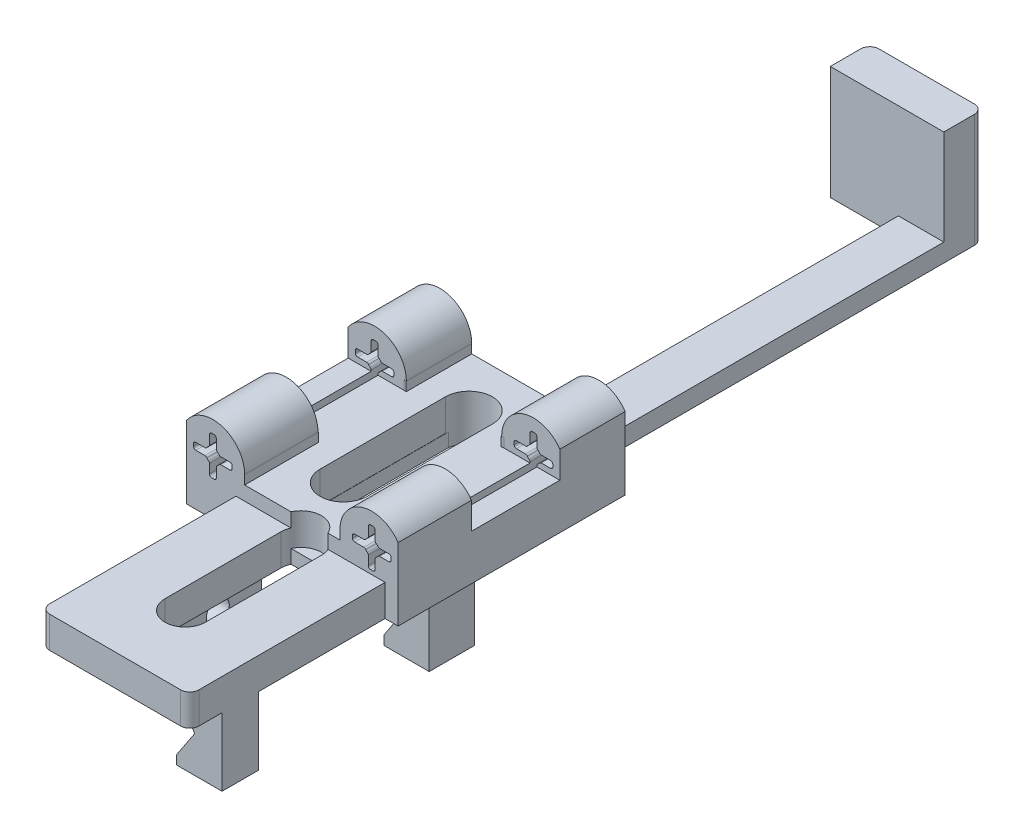
SolidWorks part; units mm, degrees
ref_plane "Спереди" through (0, 0, 0) normal (0, 0, 1) x (1, 0, 0)
ref_plane "Сверху" through (0, 0, 0) normal (0, 1, 0) x (1, 0, 0)
ref_plane "Справа" through (0, 0, 0) normal (1, 0, 0) x (0, 0, -1)
sketch "Эскиз1" plane through (0, 0, 0) normal (0, 0, 1) x (1, 0, 0)
  line L0 (19.0011, -5) -> (13.1937, -5)
  line L1 (17.2564, -4.2433) -> (15.2847, -4.2433)
  line L2 (15.2853, -5.7567) -> (17.2564, -5.7567)
  line L3 (18.2444, -6.7448) -> (18.2444, -8.7164)
  line L5 (19.2579, -9.2566) -> (18.7444, -9.2566)
  line L7 (19.7579, -8.7158) -> (19.7579, -6.7448)
  line L10 (13.1937, -5) -> (54.9814, -5)
  line L12 (13.1937, -14) -> (59.7886, -14)
  line L15 (26.0011, -5) -> (54.9814, -5)
  line L16 (20.7459, -5.7567) -> (22.7175, -5.7567)
  line L17 (13.1937, -5) -> (59.7886, -5)
  line L18 (23.2577, -4.7433) -> (23.2577, -5.2567)
  line L19 (22.717, -4.2433) -> (20.7459, -4.2433)
  line L20 (19.7579, -3.2552) -> (19.7579, -1.2836)
  line L21 (18.7444, -0.7434) -> (19.2579, -0.7434)
  line L22 (18.2444, -1.2842) -> (18.2444, -3.2552)
  line L26 (36.4911, -5) -> (36.4911, 5.7065)
  line L27 (59.7886, -5) -> (59.7886, -1.0919)
  line L28 (15.2853, -4.9459) -> (15.2853, -5)
  line L30 (15.2853, -4.9459) -> (14.7446, -4.9472)
  line L31 (13.1937, -5) -> (13.1937, -1.0919)
  line L32 (55.7259, -4.2433) -> (57.6975, -4.2433)
  line L33 (57.7377, -5.7567) -> (57.697, -5.7567)
  line L34 (58.2377, -4.9472) -> (58.2377, -5.2567)
  line L35 (58.2377, -5.2567) -> (58.2377, -4.7433)
  line L36 (52.2364, -5.7567) -> (50.2647, -5.7567)
  line L37 (53.2244, -8.7158) -> (53.2244, -6.7448)
  line L39 (53.7244, -9.2566) -> (54.2379, -9.2566)
  line L40 (54.7379, -6.7448) -> (54.7379, -8.7164)
  line L41 (57.697, -5.7567) -> (55.7259, -5.7567)
  line L42 (49.7246, -4.7433) -> (49.7246, -5.2567)
  line L43 (54.2379, -0.7434) -> (53.7244, -0.7434)
  line L44 (53.2244, -3.2552) -> (53.2244, -1.2836)
  line L45 (50.2653, -4.2433) -> (52.2364, -4.2433)
  line L46 (54.7379, -1.2842) -> (54.7379, -3.2552)
  line L47 (22.717, -4.2433) -> (22.7577, -4.2433)
  line L48 (14.7446, -5.2567) -> (14.7446, -4.7433)
  line L49 (22.7175, -5.7567) -> (22.7577, -5.7567)
  line L50 (19.7579, -1.2434) -> (19.7579, -1.2836)
  line L51 (18.2444, -1.2434) -> (18.2444, -1.2842)
  line L52 (15.2446, -4.2433) -> (15.2847, -4.2433)
  line L54 (14.7446, -4.9472) -> (14.7446, -5.2567)
  line L55 (15.2446, -5.7567) -> (15.2853, -5.7567)
  line L56 (19.7579, -8.7158) -> (19.7579, -8.7566)
  line L58 (18.2444, -8.7164) -> (18.2444, -8.7566)
  line L59 (53.2244, -1.2434) -> (53.2244, -1.2836)
  line L60 (54.7379, -1.2434) -> (54.7379, -1.2842)
  line L61 (57.6975, -4.2433) -> (57.7377, -4.2433)
  line L63 (54.7379, -8.7164) -> (54.7378, -8.7666)
  line L64 (53.2244, -8.7158) -> (53.2244, -8.7566)
  line L65 (50.2246, -5.7567) -> (50.2647, -5.7567)
  line L66 (50.2246, -4.2433) -> (50.2625, -4.2433)
  line L67 (50.2625, -4.2433) -> (50.2653, -4.2433)
  line L68 (12.9937, -5) -> (13.0169, -5)
  line L69 (13.1937, -5) -> (13.1937, -14)
  line L70 (59.7886, -5) -> (59.7886, -14)
  arc A0 (18.0366, -3.6609) -> (17.6621, -4.0355) centre (19.0011, -5) ccw
  arc A1 (26.0011, -5) -> (13.1937, -1.0919) centre (19.0011, -5) ccw
  arc A2 (14.7446, -4.7433) -> (15.2446, -4.2433) centre (15.2446, -4.7433) cw
  arc A3 (14.7446, -5.2567) -> (15.2446, -5.7567) centre (15.2446, -5.2567) ccw
  arc A4 (17.6621, -4.0355) -> (17.2564, -4.2433) centre (17.2564, -3.7433) cw
  arc A5 (18.0366, -3.6609) -> (18.2444, -3.2552) centre (17.7444, -3.2552) ccw
  arc A6 (17.6621, -5.9645) -> (17.2564, -5.7567) centre (17.2564, -6.2567) ccw
  arc A7 (17.6621, -5.9645) -> (18.0366, -6.3391) centre (19.0011, -5) ccw
  arc A8 (18.0366, -6.3391) -> (18.2444, -6.7448) centre (17.7444, -6.7448) cw
  arc A9 (18.7444, -9.2566) -> (18.2444, -8.7566) centre (18.7444, -8.7566) cw
  arc A10 (19.2579, -9.2566) -> (19.7579, -8.7566) centre (19.2579, -8.7566) ccw
  arc A11 (19.9656, -6.3391) -> (19.7579, -6.7448) centre (20.2579, -6.7448) ccw
  arc A12 (19.9656, -6.3391) -> (20.3402, -5.9645) centre (19.0011, -5) ccw
  arc A13 (20.3402, -5.9645) -> (20.7459, -5.7567) centre (20.7459, -6.2567) cw
  arc A14 (23.2577, -5.2567) -> (22.7577, -5.7567) centre (22.7577, -5.2567) cw
  arc A15 (23.2577, -4.7433) -> (22.7577, -4.2433) centre (22.7577, -4.7433) ccw
  arc A16 (19.2579, -0.7434) -> (19.7579, -1.2434) centre (19.2579, -1.2434) cw
  arc A17 (18.7444, -0.7434) -> (18.2444, -1.2434) centre (18.7444, -1.2434) ccw
  arc A18 (55.3202, -4.0355) -> (55.7259, -4.2433) centre (55.7259, -3.7433) ccw
  arc A19 (46.9811, -5) -> (59.7886, -1.0919) centre (53.9811, -5) cw
  arc A20 (58.2377, -4.7433) -> (57.7377, -4.2433) centre (57.7377, -4.7433) ccw
  arc A21 (49.7246, -5.2567) -> (50.2246, -5.7567) centre (50.2246, -5.2567) ccw
  arc A22 (52.6421, -5.9645) -> (52.2364, -5.7567) centre (52.2364, -6.2567) ccw
  arc A23 (53.0166, -6.3391) -> (52.6421, -5.9645) centre (53.9811, -5) cw
  arc A24 (53.0166, -6.3391) -> (53.2244, -6.7448) centre (52.7244, -6.7448) cw
  arc A25 (53.7244, -9.2566) -> (53.2244, -8.7566) centre (53.7244, -8.7566) cw
  arc A26 (54.2379, -9.2566) -> (54.7379, -8.7566) centre (54.2379, -8.7566) ccw
  arc A27 (54.9456, -6.3391) -> (54.7379, -6.7448) centre (55.2379, -6.7448) ccw
  arc A28 (20.3402, -4.0355) -> (20.7459, -4.2433) centre (20.7459, -3.7433) ccw
  arc A29 (20.3402, -4.0355) -> (19.9656, -3.6609) centre (19.0011, -5) ccw
  arc A30 (19.9656, -3.6609) -> (19.7579, -3.2552) centre (20.2579, -3.2552) cw
  arc A31 (55.3202, -5.9645) -> (54.9456, -6.3391) centre (53.9811, -5) cw
  arc A32 (55.3202, -5.9645) -> (55.7259, -5.7567) centre (55.7259, -6.2567) cw
  arc A33 (58.2377, -5.2567) -> (57.7377, -5.7567) centre (57.7377, -5.2567) cw
  arc A34 (53.0166, -3.6609) -> (53.2244, -3.2552) centre (52.7244, -3.2552) ccw
  arc A35 (52.6421, -4.0355) -> (53.0166, -3.6609) centre (53.9811, -5) cw
  arc A36 (52.6421, -4.0355) -> (52.2364, -4.2433) centre (52.2364, -3.7433) cw
  arc A37 (54.2379, -0.7434) -> (54.7379, -1.2434) centre (54.2379, -1.2434) cw
  arc A38 (53.7244, -0.7434) -> (53.2244, -1.2434) centre (53.7244, -1.2434) ccw
  arc A39 (49.7246, -4.7433) -> (50.2246, -4.2433) centre (50.2246, -4.7433) cw
  arc A40 (54.9456, -3.6609) -> (54.7379, -3.2552) centre (55.2379, -3.2552) cw
  arc A41 (54.9456, -3.6609) -> (55.3202, -4.0355) centre (53.9811, -5) cw
  point P49 (19, -5)
  point P59 (19.7579, -3.6479)
  point P78 (19.0011, -5)
  point P111 (19.0011, -5)
  point P146 (53.2244, -3.6479)
  dimension "D1" = 0.5
  dimension "D2" = 0.5
  dimension "D3" = 4
  dimension "D4" = 0.5
  dimension "D5" = 4
extrude "Бобышка-Вытянуть1" add sketch "Эскиз1" along normal blind 50
ref_plane "Плоскость1" through (0, 5, 0) normal (0, 1, 0) x (1, 0, 0)
sketch "Эскиз3" plane through (0, 5, 0) normal (0, 1, 0) x (1, 0, 0)
  line L1 (7.4576, -14.3929) -> (74.5504, -14.3929)
  line L2 (7.4576, -14.3929) -> (7.4576, -33.8454)
  line L3 (7.4576, -33.8454) -> (74.5504, -33.8454)
  line L4 (74.5504, -14.3929) -> (74.5504, -33.8454)
extrude "Вырез-Вытянуть1" cut sketch "Эскиз3" against normal blind 10
ref_plane "Плоскость2" through (0, 5, 0) normal (0, 1, 0) x (1, 0, 0)
sketch "Эскиз4" plane through (0, 5, 0) normal (0, 1, 0) x (1, 0, 0)
  line L0 (12, -14.3929) -> (25.4537, -14.3929)
  line L1 (12, -33.8454) -> (25.4537, -33.8454)
  line L2 (27.4537, -31.8454) -> (27.4537, -16.3929)
  line L3 (12, -14.3929) -> (9.4232, -14.3929)
  line L4 (9.4232, -48) -> (9.4232, -2) construction
  line L5 (9.4232, -14.3929) -> (9.4232, -33.8454)
  line L6 (9.4232, -33.8454) -> (12, -33.8454)
  line L7 (36.4911, -1000) -> (36.4911, 49000) construction
  line L8 (26.0011, 0) -> (46.9811, 0) construction
  line L9 (63.559, -33.8454) -> (60.9823, -33.8454)
  line L10 (60.9823, -33.8454) -> (47.5286, -33.8454)
  line L11 (45.5286, -31.8454) -> (45.5286, -16.3929)
  line L12 (60.9823, -14.3929) -> (47.5286, -14.3929)
  line L13 (60.9823, -14.3929) -> (63.559, -14.3929)
  line L14 (63.559, -14.3929) -> (63.559, -33.8454)
  arc A0 (45.5286, -31.8454) -> (47.5286, -33.8454) centre (47.5286, -31.8454) ccw
  arc A1 (45.5286, -16.3929) -> (47.5286, -14.3929) centre (47.5286, -16.3929) cw
  arc A2 (25.4537, -33.8454) -> (27.4537, -31.8454) centre (25.4537, -31.8454) ccw
  arc A3 (27.4537, -16.3929) -> (25.4537, -14.3929) centre (25.4537, -16.3929) ccw
  point P15 (36.4911, 0)
  point P23 (45.5286, -33.8454)
  point P26 (45.5286, -14.3929)
  point P29 (27.4537, -33.8454)
  point P32 (27.4537, -14.3929)
  dimension "D1" = 2
extrude "Вырез-Вытянуть2" cut sketch "Эскиз4" against normal blind 12
sketch "Эскиз5" plane through (0, 0, 50) normal (0, 0, 1) x (1, 0, 0)
  line L0 (24.0789, -14) -> (24.0789, -10.1)
  line L1 (13.1937, -14) -> (59.7886, -14) construction
  line L2 (24.0789, -10.1) -> (56.9191, -10.1)
  line L3 (56.9191, -10.1) -> (56.9191, -14)
  line L7 (24.0789, -14) -> (24.0789, -17.0125)
  line L8 (24.0789, -17.0125) -> (56.9191, -17.0125)
  line L9 (56.9191, -14) -> (56.9191, -17.0125)
extrude "Бобышка-Вытянуть2" add sketch "Эскиз5" along normal blind 43
sketch "Эскиз7" plane through (0, 5, 0) normal (0, 1, 0) x (1, 0, 0)
  line L0 (56.9191, -50) -> (24.0789, -50) construction
  line L1 (26.0011, 0) -> (46.972, 0)
  line L2 (26.0011, 0) -> (26.0011, -50)
  line L3 (26.0011, -50) -> (46.972, -50)
  line L4 (46.972, 0) -> (46.972, -50)
  line L5 (26.0011, -50) -> (46.9811, -50) construction
extrude "Вырез-Вытянуть3" cut sketch "Эскиз7" against normal blind 12
ref_plane "Плоскость4" through (0, -24, 0) normal (0, -1, 0) x (-1, 0, 0)
sketch "Эскиз9" plane through (0, -24, 0) normal (0, -1, 0) x (-1, 0, 0)
  line L0 (-24.0789, -114.8996) -> (-24.0789, -69.8111)
  line L1 (-24.0789, -120) -> (-24.0789, -50) construction
  line L2 (-24.0789, -69.8111) -> (-56.9191, -69.8111)
  line L3 (-56.9191, -120) -> (-56.9191, -50) construction
  line L4 (-56.9191, -69.8111) -> (-56.9191, -114.8996)
  line L5 (-56.9191, -114.8996) -> (-24.0789, -114.8996)
ref_plane "Плоскость5" through (0, -14, 0) normal (0, -1, 0) x (-1, 0, 0)
sketch "Эскиз10" plane through (0, -14, 0) normal (0, -1, 0) x (-1, 0, 0)
  line L5 (-24.0789, -69.8412) -> (-24.0789, -50.4965)
  line L6 (-24.0789, -50.4965) -> (-30.2022, -50.4965)
  line L7 (-30.2022, -50.4965) -> (-30.2022, -69.8412)
  line L8 (-30.2022, -69.8412) -> (-24.0789, -69.8412)
  line L9 (-24.0789, -69.8412) -> (-24.0789, -50.4965)
extrude "Бобышка-Вытянуть4" add sketch "Эскиз10" along normal blind 18 contours L7 L8 L5 L6
sketch "Эскиз15" plane through (0, 0, 0) normal (0, 0, -1) x (-1, 0, 0)
  line L0 (-61.3072, -14) -> (-41.1958, -14)
  line L1 (-25.6272, -14) -> (25.6272, -14) construction
  line L2 (-53.6559, -10) -> (-43.6559, -10)
  line L3 (-43.6559, -10) -> (-43.6559, -14)
  line L4 (-43.6559, -14) -> (-53.6559, -14)
  line L5 (-34.1958, -14) -> (-49.6559, -14)
  line L8 (-33.1958, -14) -> (-49.6559, -14)
  line L9 (-49.6559, -10) -> (-53.6559, -10)
  line L10 (-53.6559, -10) -> (-53.6559, -14)
  line L11 (-53.6559, -14) -> (-49.6559, -14)
extrude "Бобышка-Вытянуть7" add sketch "Эскиз15" along normal blind 85 contours L2 L10 L0 L4 L3
sketch "Эскиз17" plane through (0, -14, 0) normal (0, -1, 0) x (1, 0, 0)
  line L0 (53.6559, -85) -> (28.6559, -85)
  line L1 (28.6559, -85) -> (28.6559, -76.2979)
  line L2 (28.6559, -76.2979) -> (53.6559, -76.2979)
  line L3 (53.6559, -85) -> (53.6559, 0) construction
  line L4 (53.6559, -76.2979) -> (53.6559, -85)
extrude "Бобышка-Вытянуть8" add sketch "Эскиз17" against normal blind 25 contours L2 L4 L0 L1
sketch "Эскиз18" plane through (0, -14, 0) normal (0, -1, 0) x (-1, 0, 0)
  line L4 (-56.9191, -69.8111) -> (-56.9191, -114.8996) construction
  line L6 (-46.9016, -40.2655) -> (-46.9016, -30.2655)
  line L12 (-46.9016, -30.2655) -> (-56.9016, -30.2655)
  line L13 (-56.9016, -30.2655) -> (-56.9016, -40.2655)
  line L14 (-56.9016, -40.2655) -> (-46.9016, -40.2655)
  line L16 (-46.9191, -77.8996) -> (-56.9191, -77.8996)
  line L17 (-46.9191, -77.8996) -> (-46.9191, -85.8996)
  line L18 (-46.9191, -85.8996) -> (-56.9191, -85.8996)
  line L19 (-56.9191, -85.8996) -> (-56.9191, -77.8996)
extrude "Бобышка-Вытянуть9" add sketch "Эскиз18" along normal blind 18
sketch "Эскиз19" plane through (0, 0, 114.8996) normal (0, 0, 1) x (1, 0, 0)
  line L0 (46.9191, -14) -> (46.9191, -18)
  line L1 (46.9191, -32) -> (46.9191, -14) construction
  line L3 (46.9191, -30) -> (44.3506, -30)
  line L4 (46.9191, -30) -> (46.9191, -36)
  line L5 (44.3506, -30) -> (44.3506, -18)
  line L6 (46.9191, -24) -> (50.9087, -24)
  line L7 (56.9191, -24) -> (24.0789, -24) construction
  line L8 (50.9087, -24) -> (46.9191, -18)
  line L9 (50.9087, -24) -> (46.9191, -30)
  line L10 (44.3506, -18) -> (46.9191, -18)
extrude "Вырез-Вытянуть4" cut sketch "Эскиз19" against normal through all
sketch "Эскиз20" plane through (24.0789, 0, 0) normal (-1, 0, 0) x (0, 0, 1)
  line L0 (-25.6272, -24) -> (25.6272, -24) construction
  circle A0 centre (60.1142, -24) radius 2.5295
  point P2 (55.4956, -21.9471)
  point P3 (0, 0)
  point P4 (55.5733, -24)
  point P7 (60.1142, -24)
extrude "Вырез-Вытянуть5" cut sketch "Эскиз20" against normal blind 10
sketch "Эскиз21" plane through (0, -14, 0) normal (0, -1, 0) x (1, 0, 0)
  line L0 (35.8092, 77.3782) -> (35.8092, 51.8512)
  line L2 (44.7529, 51.8512) -> (44.7529, 77.3782)
  arc A0 (44.7529, 77.3782) -> (35.8092, 77.3782) centre (40.281, 77.3782) ccw
  arc A1 (35.8092, 51.8512) -> (44.7529, 51.8512) centre (40.281, 51.8512) ccw
  point P1 (0, 0)
  point P5 (39.9134, 62.14)
  point P6 (40.1126, 83.4685)
  point P9 (0, 0)
  point P10 (0, 0)
  point P11 (40.0984, 55.8969)
  point P12 (0, 0)
  point P13 (40.1931, 77.3782)
  point P14 (40.281, 51.8512)
extrude "Вырез-Вытянуть6" cut sketch "Эскиз21" against normal through all both and the other way through all
fillet "Скругление9" radius 2 2 edges at (24.0789, -13.5563, 93) (56.9191, -13.5563, 93)
sketch "Эскиз22" plane through (0, -14, 0) normal (0, -1, 0) x (1, 0, 0)
  line L0 (31.2765, 38.6814) -> (31.2765, 11.0875)
  line L1 (31.2765, 38.6814) -> (31.2765, 11.0875)
  line L2 (41.6492, 11.0875) -> (41.6492, 38.6814)
  line L3 (41.6492, 11.0875) -> (31.2765, 11.0875)
  line L4 (41.6492, 11.0875) -> (41.6492, 38.6814)
  line L5 (31.2765, 38.6814) -> (41.6492, 38.6814)
  arc A0 (41.6492, 38.6814) -> (31.2765, 38.6814) centre (36.4629, 38.6814) ccw
  arc A1 (31.2765, 11.0875) -> (41.6492, 11.0875) centre (36.4629, 11.0875) ccw
fillet "Скругление10" radius 2 2 edges at (28.6559, -1.5, -85) (53.6559, -1.5, -85)
sketch "Эскиз23" plane through (0, 0, 50) normal (0, 0, -1) x (-1, 0, 0)
  line L0 (-24.0789, -17.0125) -> (-13.2028, -17.0125)
  line L1 (-13.2028, -17.0125) -> (-13.1937, -14)
  line L2 (-13.1937, -14) -> (-59.7886, -14)
  line L3 (-59.7886, -14) -> (-59.7886, -17.0125)
  line L4 (-24.0789, -17.0125) -> (-59.7886, -17.0125)
extrude "Бобышка-Вытянуть10" add sketch "Эскиз23" along normal blind 50
extrude "Вырез-Вытянуть8" cut sketch "Эскиз22" against normal blind 50 contours L5 A0 | L5 L0 L3 L2 | L3 A1
sketch "Эскиз24" plane through (0, -14, 0) normal (0, 1, 0) x (1, 0, 0)
  line L1 (31.3129, -10.4746) -> (41.6492, -10.4746)
  line L2 (31.3129, -10.4746) -> (31.3129, -38.6814)
  line L3 (31.3129, -38.6814) -> (41.6492, -38.6814)
  line L4 (41.6492, -10.4746) -> (41.6492, -38.6814)
  arc A0 (41.6492, -11.0875) -> (31.2765, -11.0875) centre (36.4629, -11.0875) ccw construction
  arc A1 (41.6492, -11.7048) -> (31.3129, -11.7048) centre (36.4811, -11.0897) ccw
  arc A3 (31.3129, -38.6814) -> (41.6492, -38.6814) centre (36.4811, -38.6814) ccw
extrude "Вырез-Вытянуть10" cut sketch "Эскиз24" against normal blind 50 contours L1 M7 | L2 L3 L4 L1 M6 M7 | L3 A3
fillet "Скругление11" radius 2 2 edges at (27.1405, -32, 50.4965) (27.1405, -32, 69.8412)
